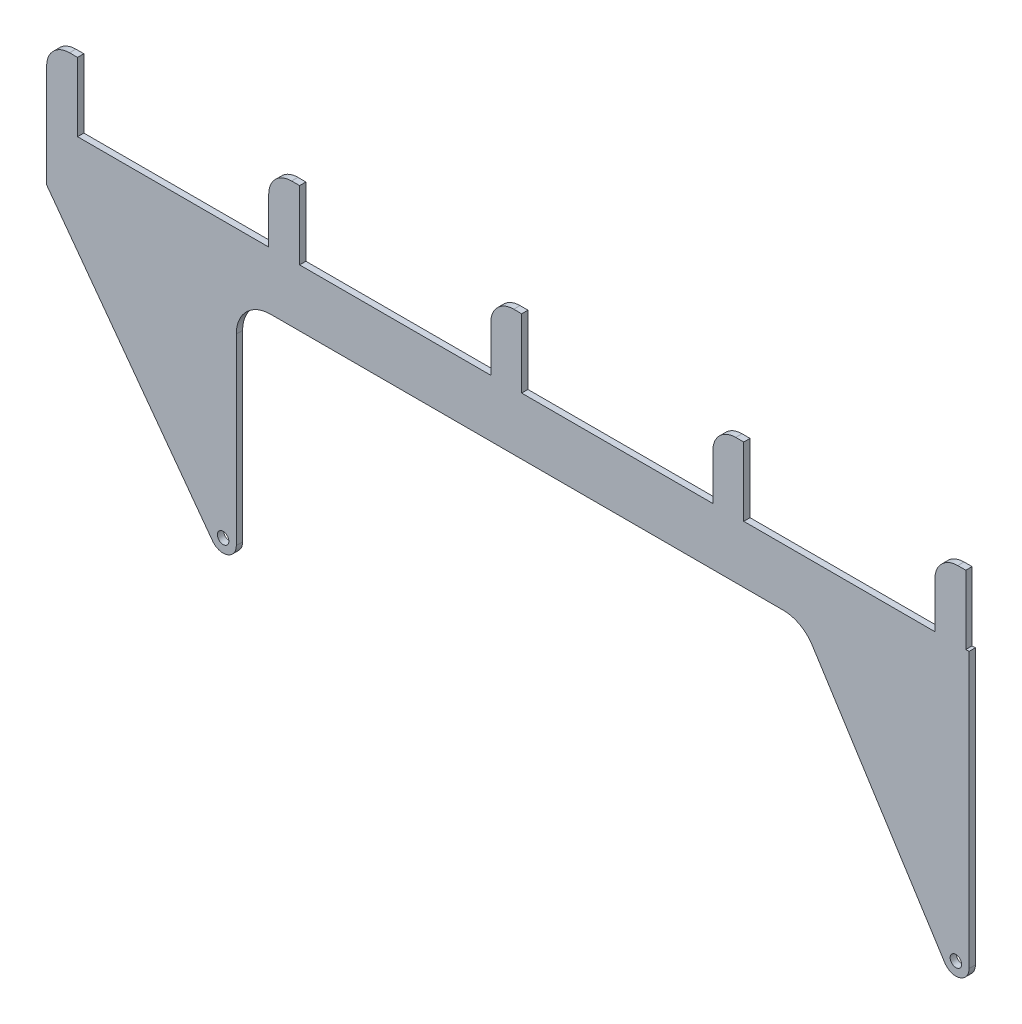
SolidWorks part; units mm, degrees
material "1.0490 (S275N)"
ref_plane "Front Plane" through (0, 0, 0) normal (0, 0, 1) x (1, 0, 0)
ref_plane "Top Plane" through (0, 0, 0) normal (0, 1, 0) x (1, 0, 0)
ref_plane "Right Plane" through (0, 0, 0) normal (1, 0, 0) x (0, 0, -1)
sketch "Sketch1" plane through (0, 0, 0) normal (0, 0, 1) x (1, 0, 0)
  line L0 (-402.92, 0) -> (-402.92, 60)
  line L1 (-402.92, 60) -> (-375.92, 60)
  line L2 (-375.92, 60) -> (-375.92, 0)
  line L3 (-375.92, 0) -> (-208.92, 0)
  line L4 (-208.92, 0) -> (-208.92, 60)
  line L5 (-208.92, 60) -> (-181.92, 60)
  line L6 (-181.92, 60) -> (-181.92, 0)
  line L7 (-181.92, 0) -> (-14.92, 0)
  line L8 (-14.92, 0) -> (-14.92, 60)
  line L9 (-14.92, 60) -> (12.08, 60)
  line L10 (12.08, 60) -> (12.08, 0)
  line L11 (12.08, 0) -> (179.08, 0)
  line L12 (179.08, 0) -> (179.08, 60)
  line L13 (179.08, 60) -> (206.08, 60)
  line L14 (206.08, 60) -> (206.08, 0)
  line L15 (206.08, 0) -> (373.08, 0)
  line L16 (373.08, 0) -> (373.08, 60)
  line L17 (373.08, 60) -> (400.08, 60)
  line L18 (400.08, 60) -> (400.08, 0)
  line L19 (400.08, 0) -> (402.92, 0)
  line L20 (-402.92, 0) -> (-402.92, -50)
  line L21 (-402.92, -50) -> (-258.0028, -246.8185)
  line L22 (402.92, 0) -> (402.92, -240)
  line L23 (-237.2423, -240) -> (-237.2423, -80)
  line L24 (-207.2423, -50) -> (240.6368, -50)
  line L25 (265.9608, -63.916) -> (381.7125, -246.1655)
  circle A0 centre (-248.7423, -240) radius 5
  circle A1 centre (391.42, -240) radius 5
  arc A2 (-258.0028, -246.8185) -> (-237.2423, -240) centre (-248.7423, -240) ccw
  arc A3 (381.7125, -246.1655) -> (402.92, -240) centre (391.42, -240) ccw
  arc A4 (240.6368, -50) -> (265.9608, -63.916) centre (240.6368, -80) cw
  arc A5 (-237.2423, -80) -> (-207.2423, -50) centre (-207.2423, -80) cw
  point P34 (0, 0)
  point P35 (494.8585, -248.9893)
  point P36 (-154.8416, -250.9586)
  point P37 (348.8435, -69.2202)
  dimension "D4" = 10
  dimension "D5" = 10
  dimension "D6" = 23
  dimension "D7" = 23
  dimension "D12" = 30
  dimension "D1" = 60
  dimension "D2" = 27
  dimension "D3" = 167
  dimension "D8" = 805.84
  dimension "D9" = 50
  dimension "D10" = 190
  dimension "D11" = 50
  dimension "D13" = 402.92
  dimension "D14" = 60
extrude "Boss-Extrude1" add sketch "Sketch1" along normal mid plane 5.5
fillet "Fillet1" radius 20 5 edges at (373.08, 60, 0) (179.08, 60, 0) (-14.92, 60, 0) (-208.92, 60, 0) (-402.92, 60, 0)
